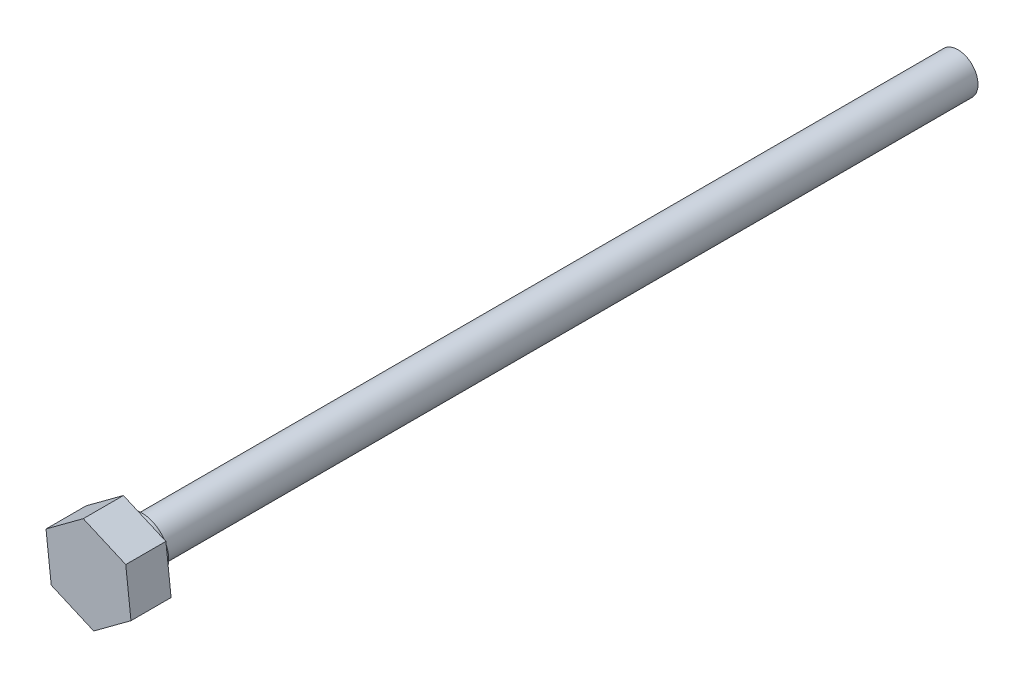
SolidWorks part; units mm, degrees
ref_plane "Front Plane" through (0, 0, 0) normal (0, 0, 1) x (1, 0, 0)
ref_plane "Top Plane" through (0, 0, 0) normal (0, 1, 0) x (1, 0, 0)
ref_plane "Right Plane" through (0, 0, 0) normal (1, 0, 0) x (0, 0, -1)
sketch "Sketch1" plane through (0, 0, 0) normal (0, 0, 1) x (1, 0, 0)
  line L1 (-3.1762, 1.3826) -> (-2.7855, -2.0594)
  line L2 (-2.7855, -2.0594) -> (0.3908, -3.442)
  line L3 (0.3908, -3.442) -> (3.1762, -1.3826)
  line L4 (3.1762, -1.3826) -> (2.7855, 2.0594)
  line L5 (2.7855, 2.0594) -> (-0.3908, 3.442)
  line L6 (-0.3908, 3.442) -> (-3.1762, 1.3826)
  circle A0 centre (0, 0) radius 3 construction
  dimension "D1" = 6
extrude "Boss-Extrude1" add sketch "Sketch1" along normal blind 3
sketch "Sketch2" plane through (0, 0, 0) normal (0, 0, 1) x (1, 0, 0)
  circle A0 centre (0, 0) radius 2
  dimension "D1" = 4
extrude "Boss-Extrude2" add sketch "Sketch2" against normal blind 1
sketch "Sketch3" plane through (0, 0, 0) normal (0, 0, 1) x (1, 0, 0)
  circle A0 centre (0, 0) radius 1.5
  dimension "D1" = 3
sketch "Sketch4" plane through (0, 0, -1) normal (0, 0, -1) x (-1, 0, 0)
  circle A0 centre (0, 0) radius 1.5
  dimension "D1" = 3
extrude "Boss-Extrude3" add sketch "Sketch4" along normal blind 61
